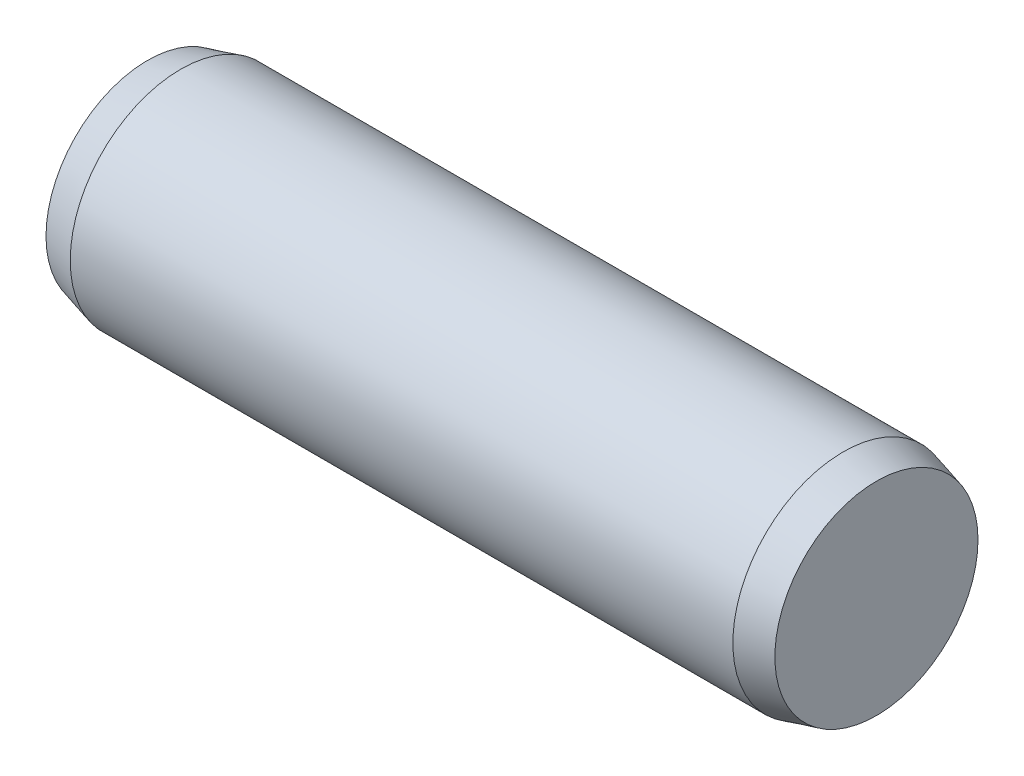
SolidWorks part; units mm, degrees
ref_plane "Front Plane" through (0, 0, 0) normal (0, 0, 1) x (1, 0, 0)
ref_plane "Top Plane" through (0, 0, 0) normal (0, 1, 0) x (1, 0, 0)
ref_plane "Right Plane" through (0, 0, 0) normal (1, 0, 0) x (0, 0, -1)
sketch "Sketch1" plane through (0, 0, 0) normal (0, 0, 1) x (1, 0, 0)
  line L0 (-6, 0) -> (6, 0) construction
  line L1 (6, 2) -> (6, -2) construction
  line L2 (-6, 2) -> (-6, -2) construction
  line L3 (6.6, 2) -> (6.6, -2) construction
  line L4 (-6.6, 2) -> (-6.6, -2) construction
  line L5 (-6, 0) -> (-6.6, 0) construction
  line L6 (6, 0) -> (6.6, 0) construction
  dimension "Dia" = 4
  dimension "Length" = 12
  dimension "C" = 0.6
  dimension "D1" = 0.6
sketch "Sketch2" plane through (0, 0, 0) normal (1, 0, 0) x (0, 0, -1)
  circle A0 centre (0, 0) radius 2
extrude "Extrude1" add sketch "Sketch2" against normal up to vertex (6 mm away) and the other way up to vertex (6 mm away) up to point (-6, 2, 0) other way up to point (6, 2, 0)
sketch "Sketch3" plane through (6, 0, 0) normal (1, 0, 0) x (0, 0, -1)
  circle A1 centre (0, 0) radius 2
  circle A2 centre (0, 0) radius 2
  dimension "D1" = 0
extrude "Extrude2" add sketch "Sketch3" along normal up to vertex (0.6 mm away) draft 15 up to point (6.6, 0, 0)
sketch "Sketch4" plane through (-6, 0, 0) normal (-1, 0, 0) x (0, 0, 1)
  circle A1 centre (0, 0) radius 2
  circle A2 centre (0, 0) radius 2
  dimension "D1" = 0
extrude "Extrude3" add sketch "Sketch4" along normal up to vertex (0.6 mm away) draft 15 up to point (-6.6, 0, 0)
equation "\"D1@Sketch1\" = \"C@Sketch1\""
